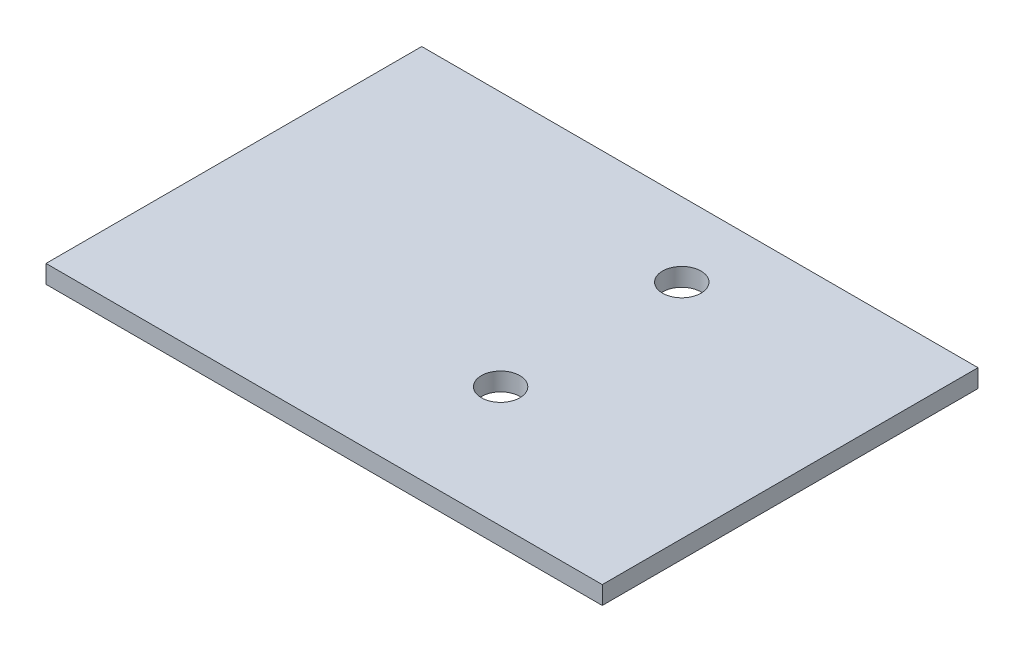
SolidWorks part; units mm, degrees
material "Custom Plastic"
ref_plane "Front Plane" through (0, 0, 0) normal (0, 0, 1) x (1, 0, 0)
ref_plane "Top Plane" through (0, 0, 0) normal (0, 1, 0) x (1, 0, 0)
ref_plane "Right Plane" through (0, 0, 0) normal (1, 0, 0) x (0, 0, -1)
sketch "Sketch1" plane through (0, 0, 0) normal (0, 1, 0) x (1, 0, 0)
  line L1 (-24.57, 16.595) -> (24.57, 16.595)
  line L2 (-24.57, 16.595) -> (-24.57, -16.595)
  line L3 (-24.57, -16.595) -> (24.57, -16.595)
  line L4 (24.57, 16.595) -> (24.57, -16.595)
  line L5 (-24.57, 16.595) -> (24.57, -16.595) construction
  line L6 (-24.57, -16.595) -> (24.57, 16.595) construction
  circle A0 centre (4.94, 10.055) radius 1.7
  circle A1 centre (4.94, -5.945) radius 1.7
  point P0 (0, 0)
  dimension "D3" = 19.63
  dimension "D4" = 19.63
  dimension "D5" = 6.54
  dimension "D6" = 16
  dimension "D7" = 3.4
  dimension "D8" = 3.4
  dimension "D1" = 33.19
  dimension "D2" = 49.14
extrude "Boss-Extrude1" add sketch "Sketch1" along normal blind 1.6
